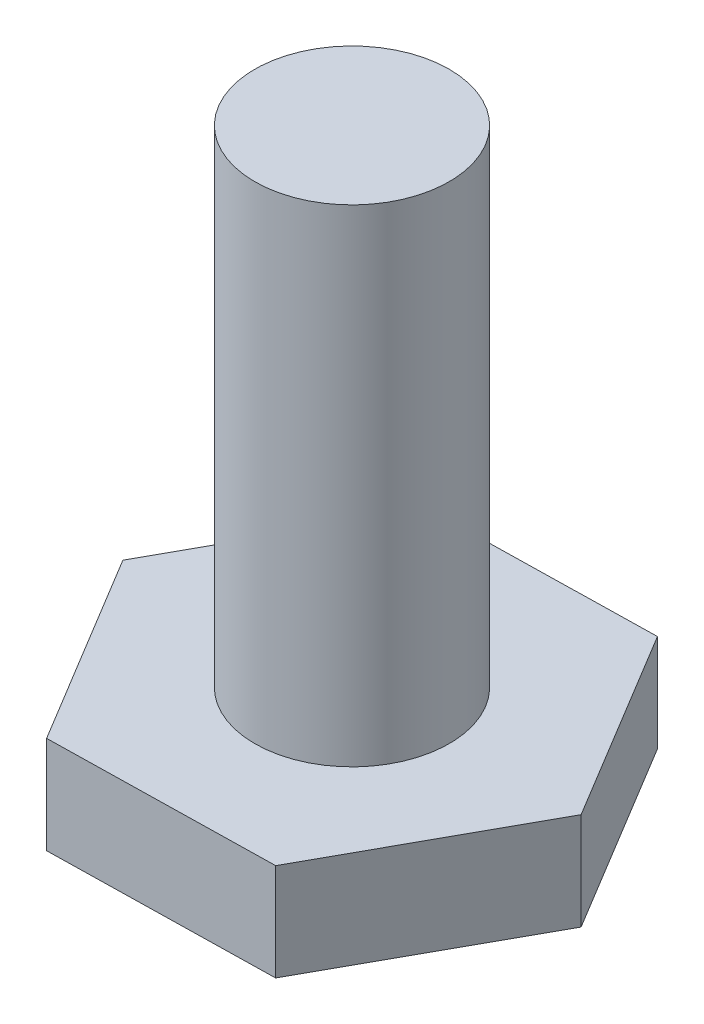
SolidWorks part; units mm, degrees
ref_plane "Front Plane" through (0, 0, 0) normal (0, 0, 1) x (1, 0, 0)
ref_plane "Top Plane" through (0, 0, 0) normal (0, 1, 0) x (1, 0, 0)
ref_plane "Right Plane" through (0, 0, 0) normal (1, 0, 0) x (0, 0, -1)
sketch "Sketch1" plane through (0, 0, 0) normal (0, 1, 0) x (1, 0, 0)
  circle A0 centre (-18.8764, -12.7107) radius 2
  dimension "D1" = 4
extrude "Boss-Extrude1" add sketch "Sketch1" along normal blind 10
sketch "Sketch2" plane through (0, 10, 0) normal (0, 1, 0) x (-1, 0, 0)
sketch "Sketch4" plane through (0, 0, 0) normal (0, -1, 0) x (1, 0, 0)
  line L1 (-16.4901, 16.6653) -> (-21.1081, 16.7546)
  line L2 (-21.1081, 16.7546) -> (-23.4943, 12.7999)
  line L3 (-23.4943, 12.7999) -> (-21.2627, 8.756)
  line L4 (-21.2627, 8.756) -> (-16.6447, 8.6668)
  line L5 (-16.6447, 8.6668) -> (-14.2585, 12.6214)
  line L6 (-14.2585, 12.6214) -> (-16.4901, 16.6653)
  circle A0 centre (-18.8764, 12.7107) radius 4 construction
  circle A1 centre (-18.8764, 12.7107) radius 2 construction
  dimension "D1" = 4
  dimension "D2" = 4
  dimension "D3" = 4
extrude "Boss-Extrude4" add sketch "Sketch4" along normal blind 2
